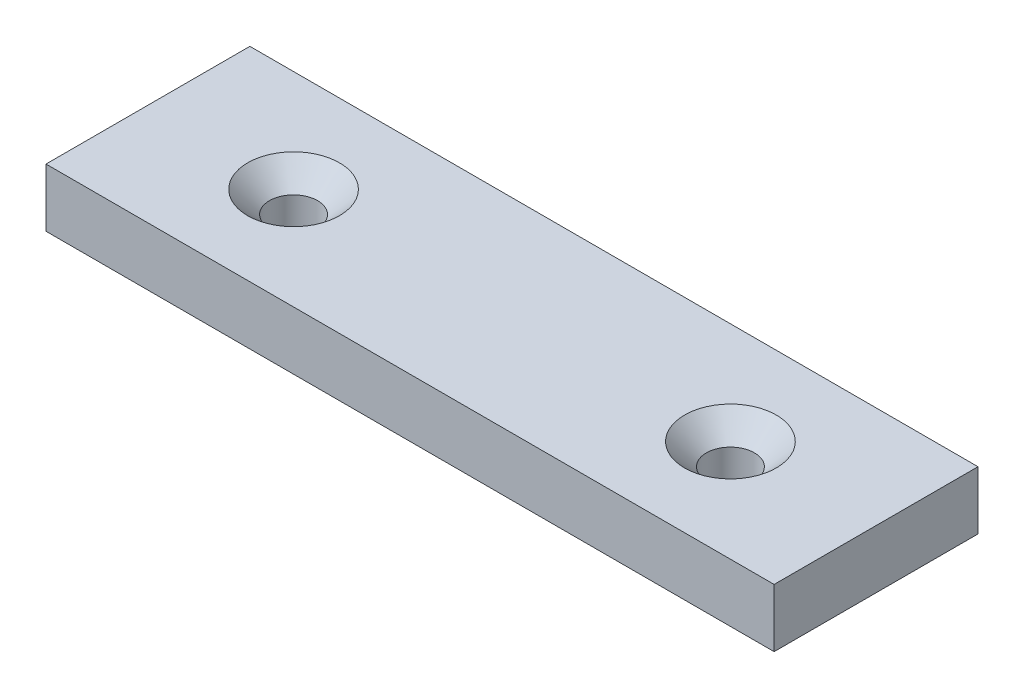
SolidWorks part; units mm, degrees
ref_plane "Front Plane" through (0, 0, 0) normal (0, 0, 1) x (1, 0, 0)
ref_plane "Top Plane" through (0, 0, 0) normal (0, 1, 0) x (1, 0, 0)
ref_plane "Right Plane" through (0, 0, 0) normal (1, 0, 0) x (0, 0, -1)
sketch "Sketch1" plane through (0, 0, 0) normal (0, 1, 0) x (1, 0, 0)
  line L1 (-50, 14) -> (50, 14)
  line L2 (-50, 14) -> (-50, -14)
  line L3 (-50, -14) -> (50, -14)
  line L4 (50, 14) -> (50, -14)
  line L5 (-50, 14) -> (50, -14) construction
  line L6 (-50, -14) -> (50, 14) construction
  point P0 (0, 0)
  dimension "D1" = 100
  dimension "D2" = 28
extrude "Boss-Extrude1" add sketch "Sketch1" along normal blind 8
sketch "Sketch2" plane through (0, 8, 0) normal (0, 1, 0) x (1, 0, 0)
  line L0 (-50, 0) -> (50, 0) construction
  line L1 (-50, 14) -> (-50, -14) construction
  line L2 (50, -14) -> (50, 14) construction
  line L3 (0, 14) -> (0, -14) construction
  line L4 (50, 14) -> (-50, 14) construction
  line L5 (-50, -14) -> (50, -14) construction
  circle A0 centre (30, 0) radius 6
  circle A1 centre (-30, 0) radius 6
  dimension "D1" = 60
hole_wizard "CSK for M6 Flat Head Machine Screw1" positions "Sketch4" profile "Sketch3" countersink size "M6" standard "ANSI Metric" end condition up to next
sketch "Sketch4" plane through (0, 8, 0) normal (0, 1, 0) x (-1, 0, 0)
  point P0 (-30, 0)
  point P3 (30, 0)
sketch "Sketch3" plane through (30, 8, 0) normal (1, 0, 0) x (0, 0, 1)
  line L0 (0, 0) -> (0, 8)
  line L1 (0, 8) -> (3.3, 8)
  line L2 (3.3, 8) -> (3.3, 3)
  line L3 (3.3, 3) -> (6.3, 0)
  line L5 (6.3, 0) -> (0, 0)
  line L6 (-3.3, 3) -> (-6.3, 0) construction
  line L11 (0, -6.35) -> (0, 107.95) construction
  dimension "Thru Hole Dia." = 6.6
  dimension "Thru Hole Depth" = 8
  dimension "Near C'Sink Dia." = 12.6
  dimension "Near C'Sink Angle" = 90
